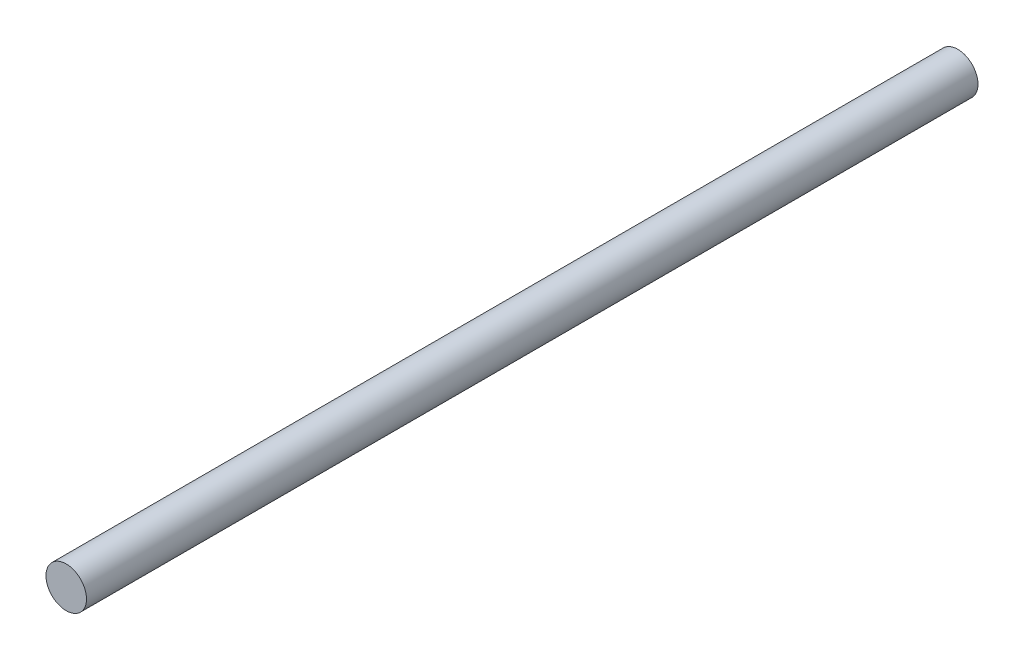
SolidWorks part; units mm, degrees
ref_plane "Front Plane" through (0, 0, 0) normal (0, 0, 1) x (1, 0, 0)
ref_plane "Top Plane" through (0, 0, 0) normal (0, 1, 0) x (1, 0, 0)
ref_plane "Right Plane" through (0, 0, 0) normal (1, 0, 0) x (0, 0, -1)
sketch "Esquisse1" plane through (0, 0, 0) normal (0, 0, 1) x (1, 0, 0)
  circle A0 centre (0, 0) radius 0.5
  dimension "D1" = 1
extrude "Boss.-Extru.1" add sketch "Esquisse1" along normal blind 22
